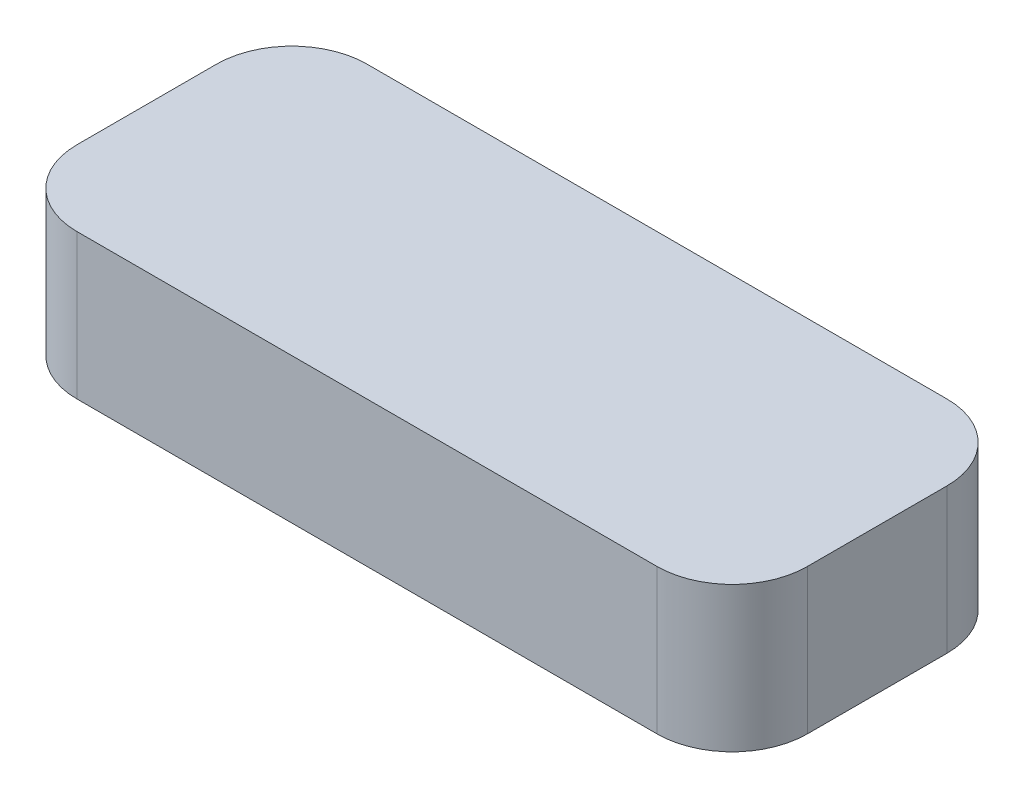
SolidWorks part; units mm, degrees
material "6061-T6 (SS)"
ref_plane "Front Plane" through (0, 0, 0) normal (0, 0, 1) x (1, 0, 0)
ref_plane "Top Plane" through (0, 0, 0) normal (0, 1, 0) x (1, 0, 0)
ref_plane "Right Plane" through (0, 0, 0) normal (1, 0, 0) x (0, 0, -1)
sketch "Sketch1" plane through (0, 0, 0) normal (0, 1, 0) x (1, 0, 0)
  line L1 (-215.9, -85.725) -> (215.9, -85.725)
  line L2 (-215.9, -85.725) -> (-215.9, 85.725)
  line L3 (-215.9, 85.725) -> (215.9, 85.725)
  line L4 (215.9, -85.725) -> (215.9, 85.725)
  line L5 (-215.9, -85.725) -> (215.9, 85.725) construction
  line L6 (-215.9, 85.725) -> (215.9, -85.725) construction
  point P0 (0, 0)
  dimension "D1" = 431.8
  dimension "D2" = 171.45
extrude "Boss-Extrude1" add sketch "Sketch1" along normal blind 85.725
sketch "Sketch2" plane through (0, 0, 0) normal (0, -1, 0) x (1, 0, 0)
  line L0 (-162.1689, -76.6864) -> (-162.1689, -85.725) construction
  line L1 (215.9, -85.725) -> (-215.9, -85.725) construction
  line L2 (-206.8614, -31.9939) -> (-215.9, -31.9939) construction
  line L3 (-215.9, -85.725) -> (-215.9, 85.725) construction
  line L4 (162.1689, -76.6864) -> (162.1689, -85.725) construction
  line L5 (206.8614, -31.9939) -> (215.9, -31.9939) construction
  line L6 (215.9, 85.725) -> (215.9, -85.725) construction
  line L7 (-162.1689, 76.6864) -> (-162.1689, 85.725) construction
  line L8 (-215.9, 85.725) -> (215.9, 85.725) construction
  line L9 (-206.8614, 31.9939) -> (-215.9, 31.9939) construction
  line L10 (206.8614, 31.9939) -> (215.9, 31.9939) construction
  line L11 (162.1689, 76.6864) -> (162.1689, 85.725)
  line L18 (162.1689, 76.6864) -> (-162.1689, 76.6864)
  line L19 (206.8614, -31.9939) -> (206.8614, 31.9939)
  line L20 (-162.1689, -76.6864) -> (162.1689, -76.6864)
  line L21 (-206.8614, 31.9939) -> (-206.8614, -31.9939)
  arc A0 (206.8614, -31.9939) -> (162.1689, -76.6864) centre (162.1689, -31.9939) cw
  arc A1 (162.1689, 76.6864) -> (206.8614, 31.9939) centre (162.1689, 31.9939) cw
  arc A2 (-162.1689, 76.6864) -> (-206.8614, 31.9939) centre (-162.1689, 31.9939) ccw
  arc A3 (-162.1689, -76.6864) -> (-206.8614, -31.9939) centre (-162.1689, -31.9939) cw
  dimension "D2" = 44.6926
extrude "Cut-Extrude1" cut sketch "Sketch2" against normal offset from surface (73.025 mm away) 12.7 contours A1 L19 A0 L20 A3 L21 A2 L18 up to face at (0, 85.725, 0)
fillet "Fillet3" radius 44.45 4 edges at (215.9, 42.8625, -85.725) (215.9, 42.8625, 85.725) (-215.9, 42.8625, 85.725) (-215.9, 42.8625, -85.725)
shell "Shell1" [suppressed] thickness 9.398
fillet "Fillet4" [suppressed] radius 0.762
equation "\"oring.277.ID\"= 11.484in"
equation "\"oring.277.A\"= 11.750in"
equation "\"oring.277.A1\"= 11.722in"
equation "\"oring.277.B\"= 11.500in"
equation "\"oring.277.B1\"= 11.528in"
equation "\"oring.277.C\"= 11.747in"
equation "\"oring.277.D\"= 11.503in"
equation "\"oring.277.G\"= 0.187in"
equation "\"D1@Sketch2\" = ( \"oring.279.A\" + \"anodize.add\" * 2 ) * PI"
equation "\"D2@Sketch2\"=12 * \"oring.279.W\" + ( \"oring.279.C.factor\" - \"oring.279.B1\" ) / 2"
equation "\"oring.277.W\"= 0.139in"
equation "\"anodize.add\"= 0.001in"
equation "\"c.factor\"= 0.00271"
equation "\"oring.277.C.factor\"= \"oring.277.C\" - \"oring.277.C\" * \"c.factor\""
equation "\"oring.279.ID\"= 12.984in"
equation "\"oring.279.A\"= 13.250in"
equation "\"oring.279.A1\"= 13.222in"
equation "\"oring.279.B\"= 13.000in"
equation "\"oring.279.B1\"= 13.028in"
equation "\"oring.279.C\"= 13.247in"
equation "\"oring.279.D\"= 13.003in"
equation "\"oring.279.G\"= 0.187in"
equation "\"oring.279.W\"= 0.139in"
equation "\"oring.279.C.factor\"= \"oring.279.C\" - \"oring.279.C\" * \"c.factor\""
